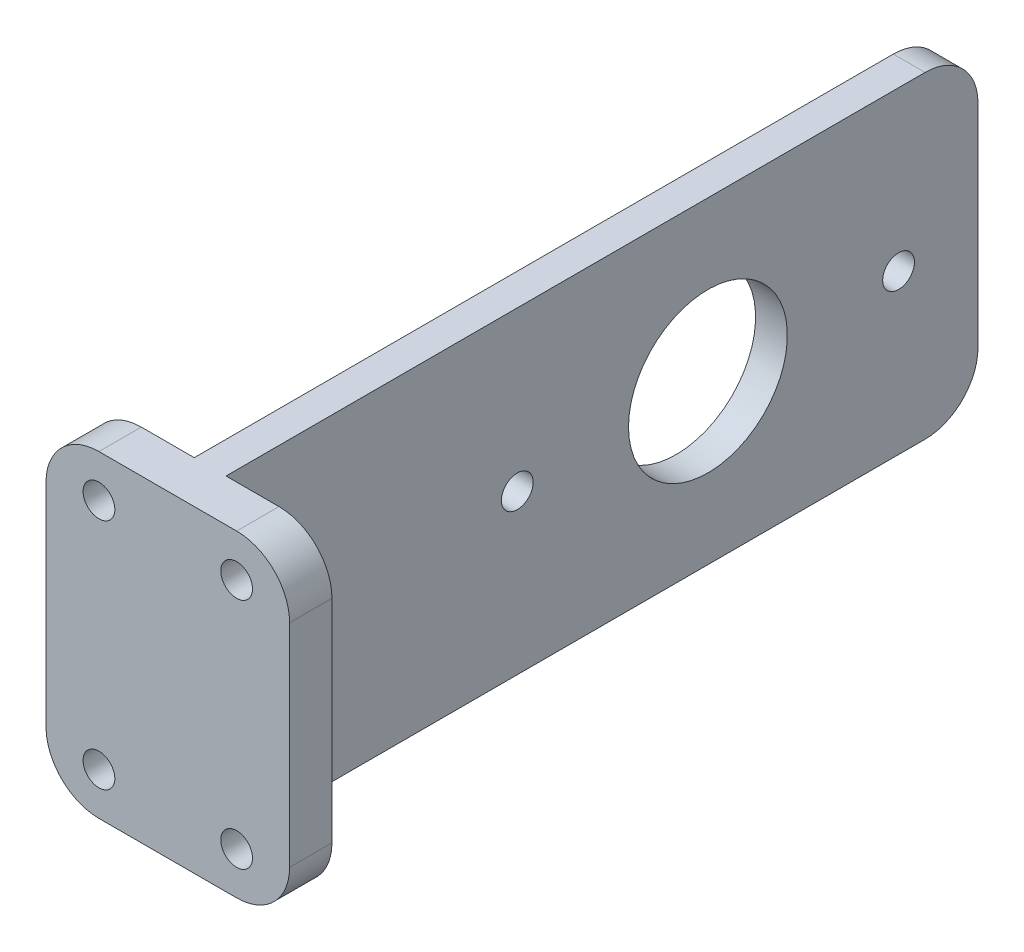
SolidWorks part; units mm, degrees
ref_plane "Front Plane" through (0, 0, 0) normal (0, 0, 1) x (1, 0, 0)
ref_plane "Top Plane" through (0, 0, 0) normal (0, 1, 0) x (1, 0, 0)
ref_plane "Right Plane" through (0, 0, 0) normal (1, 0, 0) x (0, 0, -1)
sketch "Sketch1" plane through (0, 0, 0) normal (0, 1, 0) x (1, 0, 0)
  line L0 (0, 35.1176) -> (0, -36.8824) construction
  line L1 (-40.3529, 0) -> (41.8824, 0) construction
  line L2 (-11.5, 4) -> (-1.5, 4)
  line L3 (-1.5, 4) -> (-1.5, 75)
  line L4 (-1.5, 75) -> (1.5, 75)
  line L5 (-11.5, 4) -> (-11.5, 0)
  line L6 (-11.5, 0) -> (11.5, 0)
  line L7 (11.5, 4) -> (11.5, 0)
  line L8 (1.5, 4) -> (1.5, 75)
  line L9 (11.5, 4) -> (1.5, 4)
  point P12 (0, 0)
  point P14 (0, 75)
  dimension "D1" = 4
  dimension "D2" = 1.5
  dimension "D3" = 71
  dimension "D4" = 10
extrude "Boss-Extrude1" add sketch "Sketch1" along normal blind 30
sketch "Sketch2" plane through (-1.5, 0, 0) normal (-1, 0, 0) x (0, 0, 1)
  line L0 (-75, 30) -> (-4, 30) construction
  line L3 (-75, 30) -> (-75, 0) construction
  circle A0 centre (-67.5, 15) radius 1.5
  circle A1 centre (-31.5, 15) radius 1.5
  circle A2 centre (-49.5, 15) radius 7.5
  dimension "D1" = 15
  dimension "D2" = 3
  dimension "D3" = 15
  dimension "D4" = 36
  dimension "D5" = 7.5
  dimension "D6" = 18
extrude "Cut-Extrude1" cut sketch "Sketch2" against normal through all
sketch "Sketch3" plane through (0, 0, 0) normal (0, 0, 1) x (1, 0, 0)
  line L0 (0, 30.8618) -> (0, -1.0393) construction
  line L1 (-21.25, 15) -> (21.7222, 15) construction
  line L2 (-11.5, 30) -> (11.5, 30) construction
  line L3 (-11.5, 30) -> (-11.5, 0) construction
  line L4 (11.5, 30) -> (11.5, 0) construction
  line L5 (-11.5, 0) -> (11.5, 0) construction
  circle A0 centre (-6.5, 26) radius 1.5
  circle A1 centre (-6.5, 4) radius 1.5
  circle A2 centre (6.5, 4) radius 1.5
  circle A3 centre (6.5, 26) radius 1.5
  dimension "D2" = 3
  dimension "D3" = 4
  dimension "D4" = 5
  dimension "D5" = 5
  dimension "D6" = 4
  dimension "D1" = 15
extrude "Cut-Extrude2" cut sketch "Sketch3" against normal through all
fillet "Fillet1" radius 5 6 edges at (-11.5, 0, -2) (-11.5, 30, -2) (11.5, 30, -2) (11.5, 0, -2) (0, 30, -75) (0, 0, -75)
